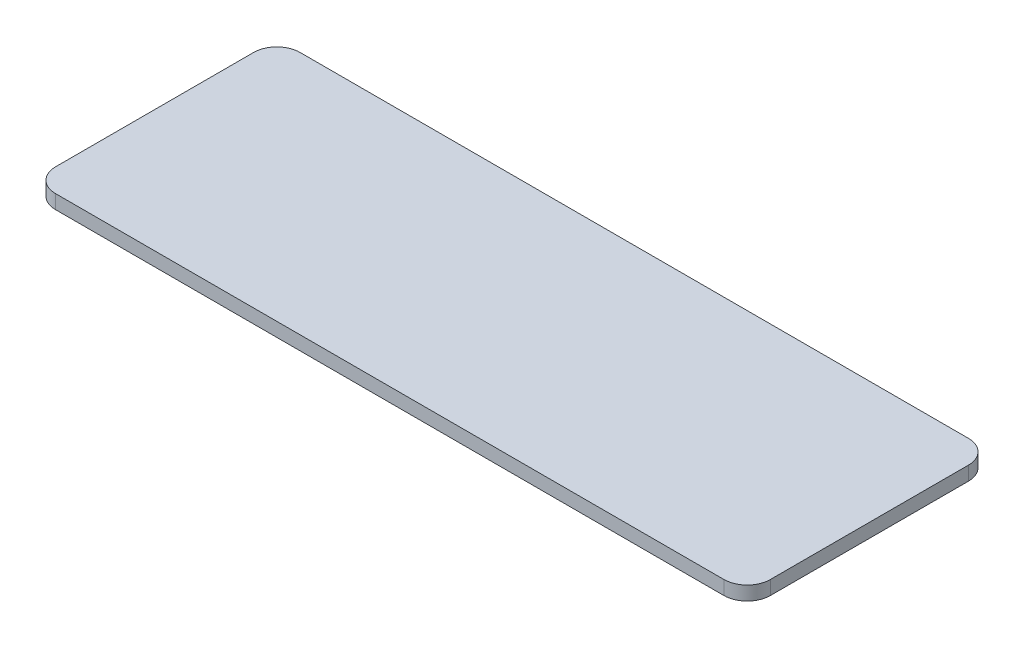
SolidWorks part; units mm, degrees
ref_plane "前视基准面" through (0, 0, 0) normal (0, 0, 1) x (1, 0, 0)
ref_plane "上视基准面" through (0, 0, 0) normal (0, 1, 0) x (1, 0, 0)
ref_plane "右视基准面" through (0, 0, 0) normal (1, 0, 0) x (0, 0, -1)
other "Configuration Table"
sketch "草图1" plane through (0, 0, 0) normal (0, 1, 0) x (1, 0, 0)
  line L1 (-36, -13.17) -> (36, -13.17)
  line L2 (-38.5, -10.67) -> (-38.5, 10.67)
  line L3 (-36, 13.17) -> (36, 13.17)
  line L4 (38.5, -10.67) -> (38.5, 10.67)
  line L5 (-38.5, -13.17) -> (38.5, 13.17) construction
  line L6 (-38.5, 13.17) -> (38.5, -13.17) construction
  arc A0 (36, 13.17) -> (38.5, 10.67) centre (36, 10.67) cw
  arc A1 (36, -13.17) -> (38.5, -10.67) centre (36, -10.67) ccw
  arc A2 (-36, -13.17) -> (-38.5, -10.67) centre (-36, -10.67) cw
  arc A3 (-38.5, 10.67) -> (-36, 13.17) centre (-36, 10.67) cw
  point P0 (0, 0)
  dimension "D3" = 2.5
  dimension "D1" = 26.34
  dimension "D2" = 77
extrude "凸台-拉伸1" add sketch "草图1" along normal blind 1.5
